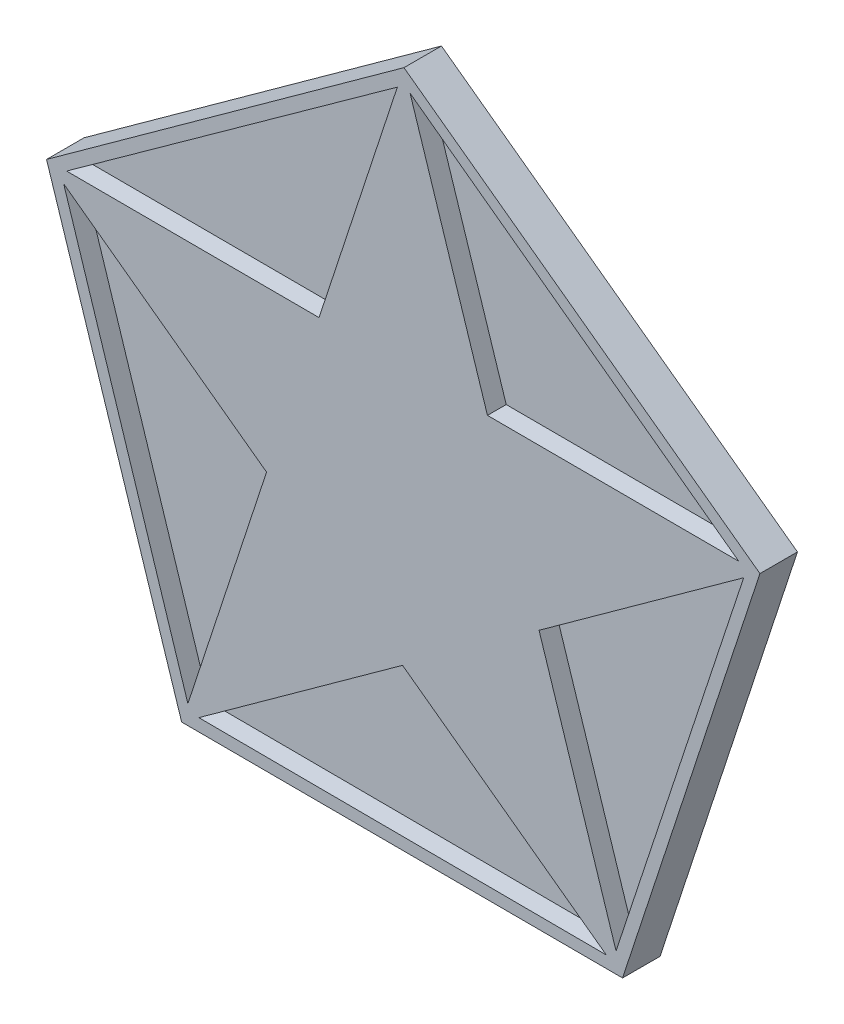
SolidWorks part; units mm, degrees
ref_plane "Alzado" through (0, 0, 0) normal (0, 0, 1) x (1, 0, 0)
ref_plane "Planta" through (0, 0, 0) normal (0, 1, 0) x (1, 0, 0)
ref_plane "Vista lateral" through (0, 0, 0) normal (1, 0, 0) x (0, 0, -1)
sketch "Croquis1" plane through (0, 0, 0) normal (0, 0, 1) x (1, 0, 0)
  line L1 (0.0275, 10) -> (-9.502, 3.1163)
  line L2 (-9.502, 3.1163) -> (-5.9001, -8.074)
  line L3 (-5.9001, -8.074) -> (5.8556, -8.1063)
  line L4 (5.8556, -8.1063) -> (9.519, 3.064)
  line L5 (9.519, 3.064) -> (0.0275, 10)
  circle A0 centre (0, 0) radius 10 construction
  circle A1 centre (0, 0) radius 8.0902 construction
  dimension "D1" = 20
  dimension "D2" = 10
extrude "Saliente-Extruir1" add sketch "Croquis1" along normal blind 1
sketch "Croquis2" plane through (0, 0, 1) normal (0, 0, 1) x (1, 0, 0)
  line L1 (0.0426, 9.6002) -> (-9.1172, 3.0071)
  line L2 (-9.1172, 3.0071) -> (-5.6773, -7.7417)
  line L3 (-5.6773, -7.7417) -> (5.6085, -7.7918)
  line L4 (5.6085, -7.7918) -> (9.1435, 2.9262)
  line L5 (9.1435, 2.9262) -> (0.0426, 9.6002)
  circle A0 centre (0, 0) radius 7.7668 construction
  dimension "D1" = 0.4
extrude "Cortar-Extruir1" cut sketch "Croquis2" against normal blind 0.5
sketch "Croquis3" plane through (0, 0, 0.5) normal (0, 0, 1) x (1, 0, 0)
  line L0 (-5.9001, -8.074) -> (-0.0105, -3.8196)
  line L1 (5.8556, -8.1063) -> (-0.0105, -3.8196)
  line L10 (0.0275, 10) -> (-2.2366, 3.0963)
  line L12 (5.8556, -8.1063) -> (3.6295, -1.1903)
  line L13 (-9.502, 3.1163) -> (-2.2366, 3.0963)
  line L14 (-3.6359, -1.1703) -> (-5.9001, -8.074)
  line L15 (-3.6359, -1.1703) -> (-9.502, 3.1163)
  line L16 (3.6295, -1.1903) -> (9.519, 3.064)
  line L17 (2.2536, 3.084) -> (0.0275, 10)
  line L18 (2.2536, 3.084) -> (9.519, 3.064)
extrude "Saliente-Extruir2" add sketch "Croquis3" along normal blind 0.5
